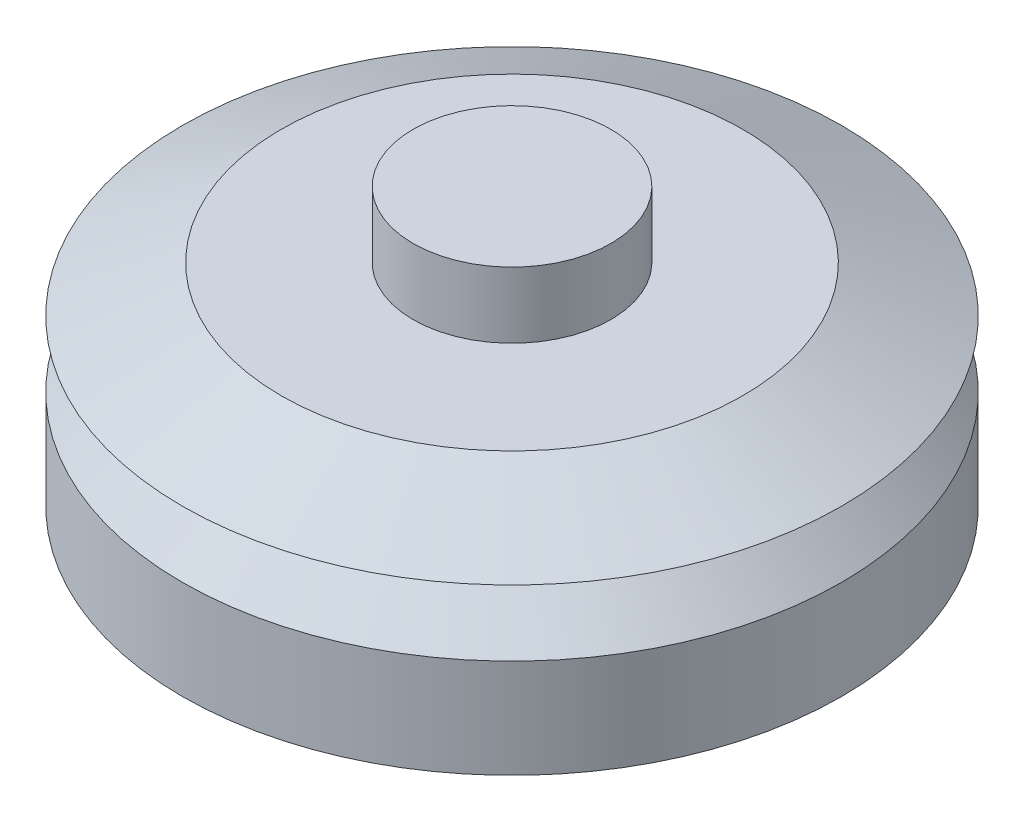
SolidWorks part; units mm, degrees
ref_plane "Front Plane" through (0, 0, 0) normal (0, 0, 1) x (1, 0, 0)
ref_plane "Top Plane" through (0, 0, 0) normal (0, 1, 0) x (1, 0, 0)
ref_plane "Right Plane" through (0, 0, 0) normal (1, 0, 0) x (0, 0, -1)
sketch "Sketch1" plane through (0, 0, 0) normal (0, 1, 0) x (1, 0, 0)
  circle A0 centre (0, 0) radius 50
  dimension "D1" = 100
extrude "Boss-Extrude1" add sketch "Sketch1" along normal blind 25
chamfer "Chamfer1" distance 10 angle 45 1 edges at (0, 25, 50)
ref_plane "Plane1" through (0, 0, 0) normal (0, -1, 0) x (-1, 0, 0)
sketch "Sketch2" plane through (0, 0, 0) normal (0, -1, 0) x (-1, 0, 0)
  line L1 (83.0719, 37.5) -> (33.0719, 37.5)
  line L2 (83.0719, 37.5) -> (83.0719, -37.5)
  line L3 (83.0719, -37.5) -> (33.0719, -37.5)
  line L5 (83.0719, 37.5) -> (50, 0) construction
  line L6 (83.0719, -37.5) -> (50, 0) construction
  circle A0 centre (0, 0) radius 50 construction
  circle A1 centre (0, 0) radius 50
  point P0 (50, 0)
  dimension "D1" = 50
  dimension "D2" = 50
  dimension "D3" = 75
sketch "Sketch7" plane through (0, 25, 0) normal (0, 1, 0) x (1, 0, 0)
  circle A0 centre (0, 0) radius 50
  dimension "D1" = 100
ref_plane "Plane3" through (0, 32, 0) normal (0, 1, 0) x (1, 0, 0)
sketch "Sketch8" plane through (0, 32, 0) normal (0, 1, 0) x (1, 0, 0)
  circle A2 centre (0, 0) radius 35
  circle A3 centre (0, 0) radius 35
  dimension "D1" = 15
loft "Loft1" add profiles "Sketch7", "Sketch8"
sketch "Sketch9" plane through (0, 32, 0) normal (0, 1, 0) x (1, 0, 0)
  circle A0 centre (0, 0) radius 15
  dimension "D1" = 30
extrude "Boss-Extrude5" add sketch "Sketch9" along normal blind 10
